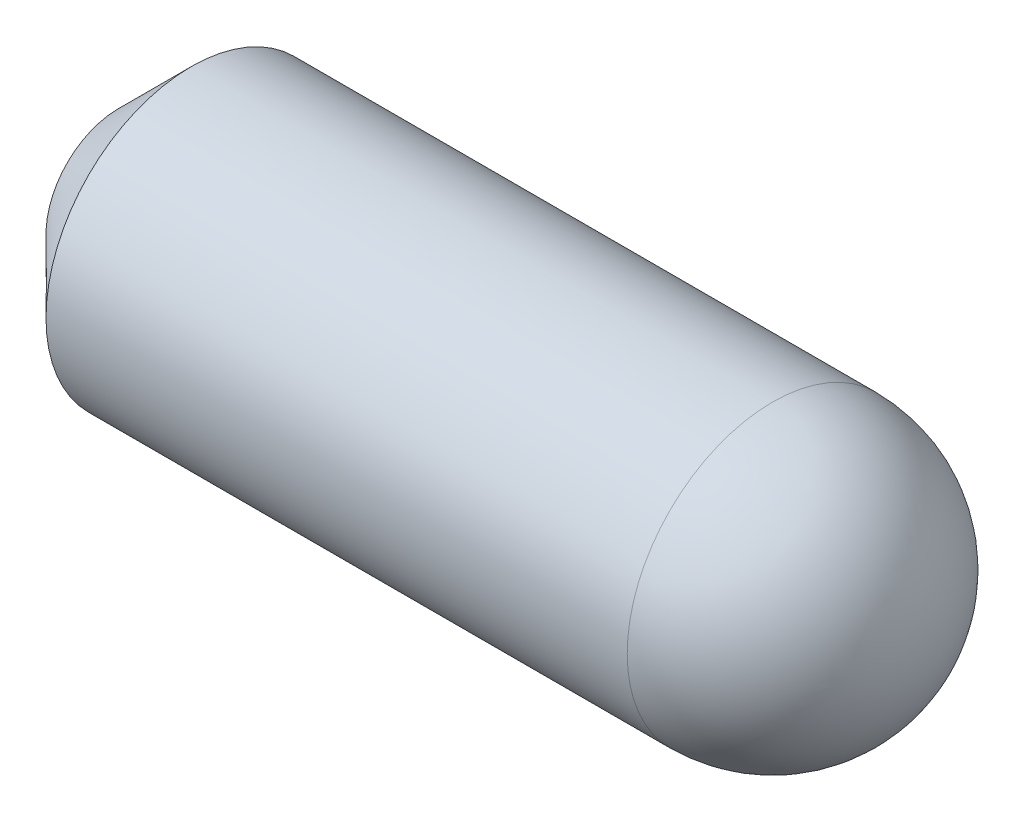
SolidWorks part; units mm, degrees
ref_plane "Front" through (0, 0, 0) normal (0, 0, 1) x (1, 0, 0)
ref_plane "Top" through (0, 0, 0) normal (0, 1, 0) x (1, 0, 0)
ref_plane "Right" through (0, 0, 0) normal (1, 0, 0) x (0, 0, -1)
sketch "Sketch1" plane through (0, 0, 0) normal (0, 0, 1) x (1, 0, 0)
  line L0 (-4.8015, 0) -> (25.8023, 0) construction
  line L2 (0, 0) -> (11, 0)
  line L3 (0, 0) -> (0, 2)
  line L4 (0, 2) -> (11, 2)
  line L5 (11, 0) -> (11, 2)
  dimension "D1" = 11
  dimension "D2" = 4
revolve "Revolve1" add sketch "Sketch1" angle 360 about L0
chamfer "Chamfer1" distance 1 angle 45 1 edges at (0, 0, 2)
fillet "Fillet1" radius 2 1 edges at (11, 0, 2)
